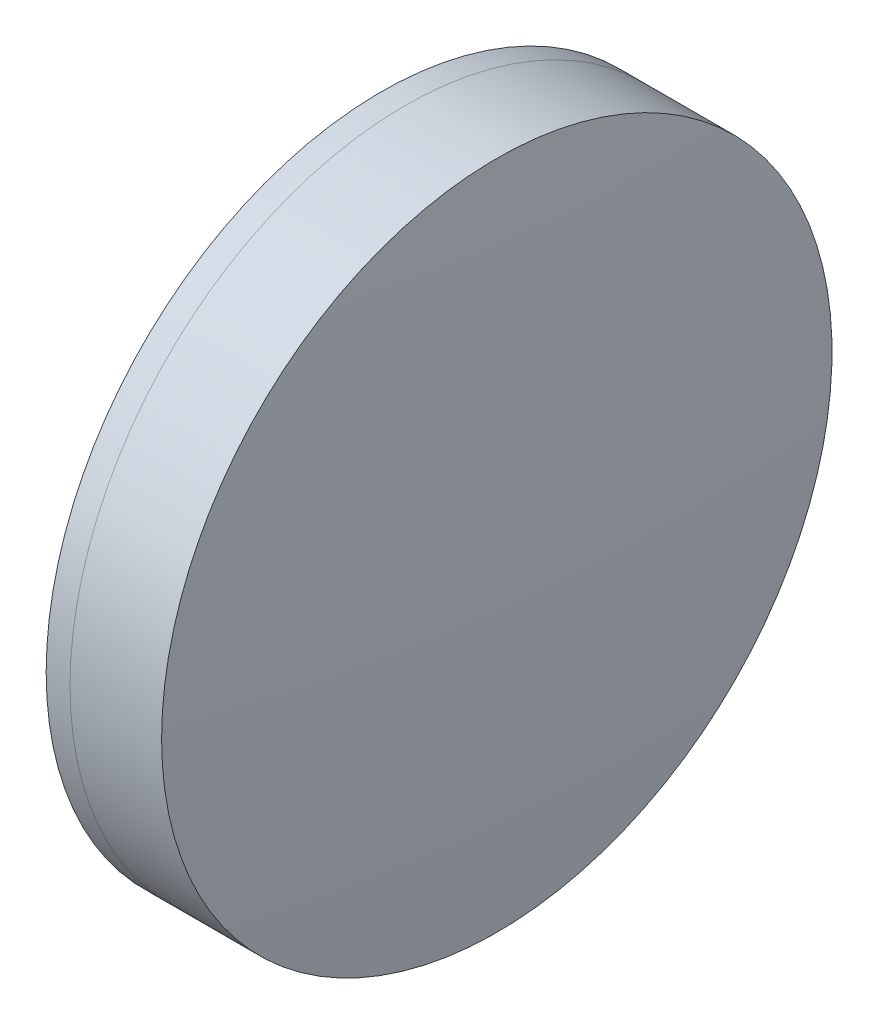
SolidWorks part; units mm, degrees
ref_plane "前视基准面" through (0, 0, 0) normal (0, 0, 1) x (1, 0, 0)
ref_plane "上视基准面" through (0, 0, 0) normal (0, 1, 0) x (1, 0, 0)
ref_plane "右视基准面" through (0, 0, 0) normal (1, 0, 0) x (0, 0, -1)
sketch "草图1" plane through (0, 0, 0) normal (0, 1, 0) x (1, 0, 0)
  line L0 (124.5233, 0) -> (646.9917, 0) construction
  line L1 (534.2585, -25.4) -> (536.0668, -25.4)
  line L2 (534.2585, 25.4) -> (536.0668, 25.4)
  arc A0 (536.0668, -25.4) -> (536.0668, 25.4) centre (486.1584, 0) ccw
  arc A1 (534.2585, 25.4) -> (534.2585, -25.4) centre (594.9584, 0) ccw
  point P10 (529.1584, 0)
  point P11 (542.1584, 0)
  dimension "D3" = 65.8
  dimension "D4" = 56
  dimension "D1" = 25.4
  dimension "D2" = 25.4
  dimension "D5" = 13
revolve "旋转1" add sketch "草图1" angle 360 about L0
sketch "草图2" plane through (0, 0, 0) normal (0, 1, 0) x (1, 0, 0)
  line L0 (-0.5519, 0) -> (622.6607, 0) construction
  line L2 (536.0668, 25.4) -> (543.0065, 25.4)
  line L3 (536.0668, -25.4) -> (543.0065, -25.4)
  arc A0 (543.0065, -25.4) -> (543.0065, 25.4) centre (263.5584, 0) ccw
  arc A1 (536.0668, -25.4) -> (536.0668, 25.4) centre (486.1584, 0) ccw construction
  arc A2 (536.0668, -25.4) -> (536.0668, 25.4) centre (486.1584, 0) ccw
  point P4 (542.1584, 0)
  point P8 (544.1584, 0)
  dimension "D1" = 280.6
  dimension "D2" = 2
revolve "旋转3" add sketch "草图2" angle 360 about L0
